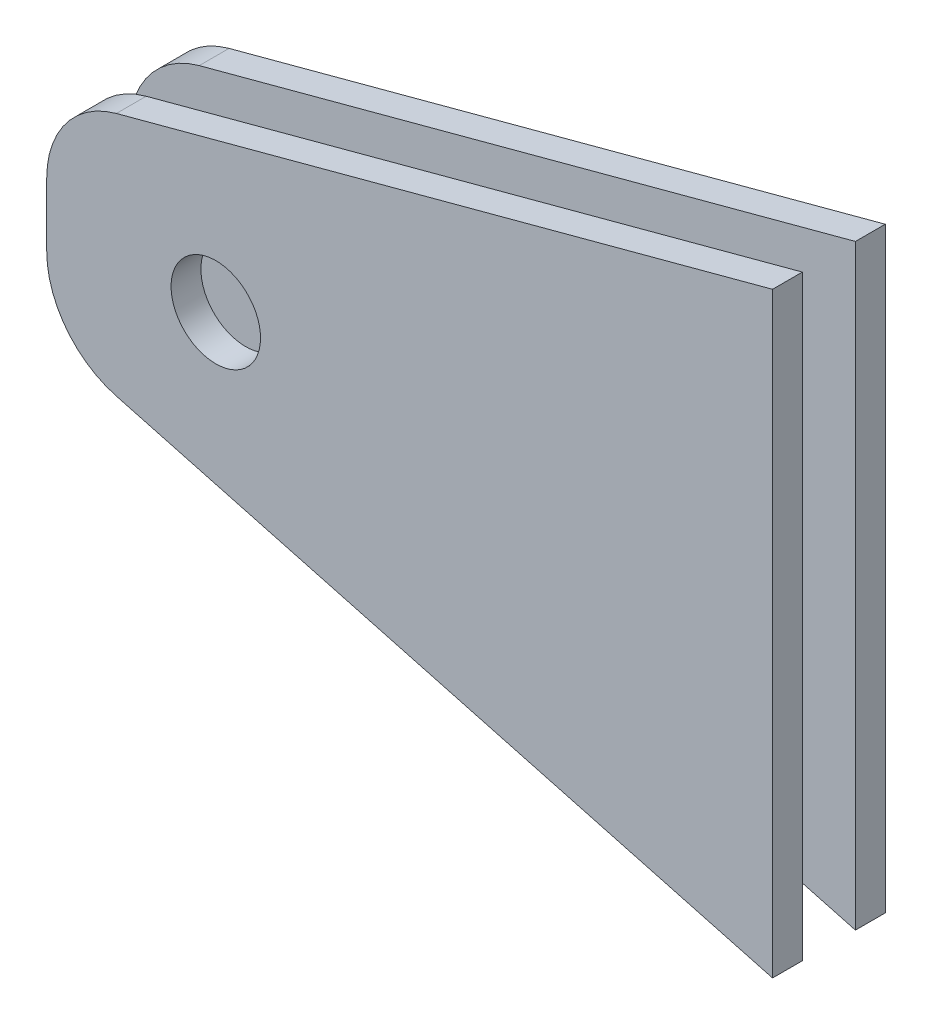
SolidWorks part; units mm, degrees
ref_plane "Alzado" through (0, 0, 0) normal (0, 0, 1) x (1, 0, 0)
ref_plane "Planta" through (0, 0, 0) normal (0, 1, 0) x (1, 0, 0)
ref_plane "Vista lateral" through (0, 0, 0) normal (1, 0, 0) x (0, 0, -1)
sketch "Croquis1" plane through (0, 0, 0) normal (0, 0, 1) x (1, 0, 0)
  line L0 (0, 0) -> (0, 63.5)
  line L1 (0, 63.5) -> (-77.2741, 42.7945)
  line L2 (0, 0) -> (-77.2741, 20.7055)
  line L3 (-77.2741, 42.7945) -> (-77.2741, 20.7055)
  dimension "D1" = 63.5
  dimension "D2" = 75
  dimension "D3" = 75
  dimension "D4" = 80
extrude "Saliente-Extruir1" add sketch "Croquis1" along normal blind 12
sketch "Croquis2" plane through (0, 0, 12) normal (0, 0, 1) x (1, 0, 0)
  line L0 (-77.2741, 31.75) -> (-59.2741, 31.75) construction
  line L1 (-77.2741, 42.7945) -> (-77.2741, 20.7055) construction
  circle A0 centre (-59.2741, 31.75) radius 4.7625
  dimension "D2" = 9.525
  dimension "D1" = 18
extrude "Cortar-Extruir1" cut sketch "Croquis2" against normal up to surface (12 mm away) up to face at (-38.637, 31.75, 0)
fillet "Redondeo1" radius 10 2 edges at (-77.2741, 20.7055, 6) (-77.2741, 42.7945, 6)
sketch "Croquis3" plane through (-77.2741, 0, 0) normal (-1, 0, 0) x (0, 0, 1)
  line L0 (0, 31.75) -> (12, 31.75) construction
  line L1 (0, 35.1212) -> (0, 28.3788) construction
  line L2 (12, 35.1212) -> (12, 28.3788) construction
  line L3 (12, 63.5) -> (12, 44.7805) construction
  line L4 (3.175, -14.9495) -> (8.825, -14.9495)
  line L5 (3.175, -14.9495) -> (3.175, 78.4495)
  line L6 (3.175, 78.4495) -> (8.825, 78.4495)
  line L7 (8.825, -14.9495) -> (8.825, 78.4495)
  line L8 (3.175, -14.9495) -> (8.825, 78.4495) construction
  line L9 (3.175, 78.4495) -> (8.825, -14.9495) construction
  point P6 (6, 31.75)
  dimension "D1" = 3.175
extrude "Cortar-Extruir2" cut sketch "Croquis3" against normal blind 100
